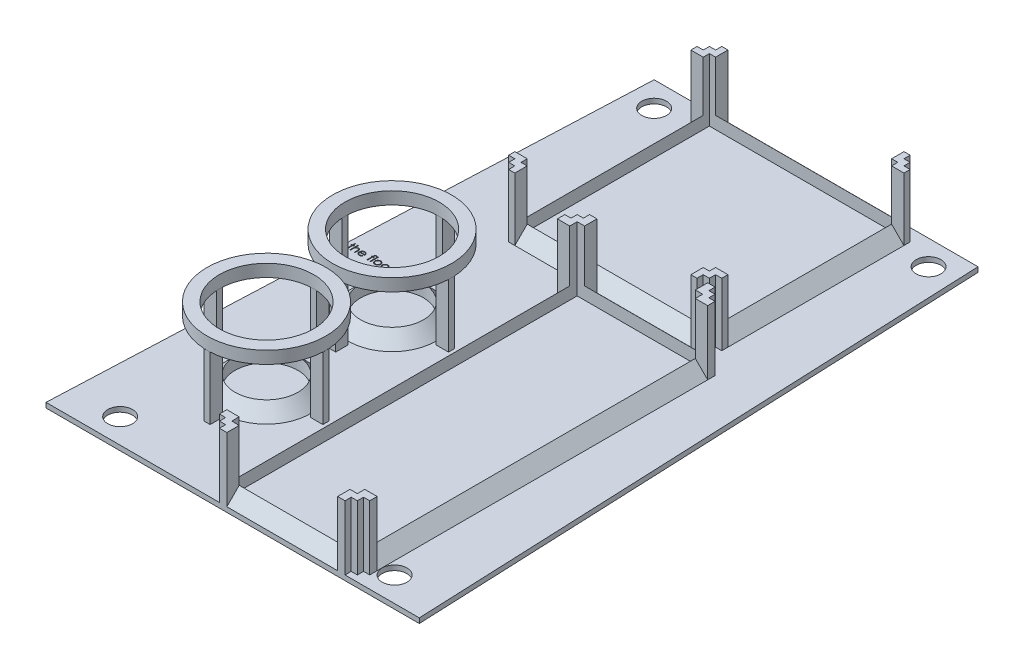
SolidWorks part; units mm, degrees
ref_plane "Front Plane" through (0, 0, 0) normal (0, 0, 1) x (1, 0, 0)
ref_plane "Top Plane" through (0, 0, 0) normal (0, 1, 0) x (1, 0, 0)
ref_plane "Right Plane" through (0, 0, 0) normal (1, 0, 0) x (0, 0, -1)
sketch "Sketch1" plane through (0, 0, 0) normal (0, 1, 0) x (1, 0, 0)
  line L0 (0, -118) -> (0, 118)
  line L1 (-65.5, 118) -> (65.5, 118)
  line L2 (-75.5, -118) -> (75.5, -118)
  line L3 (-65.5, 118) -> (-75.5, -118)
  line L4 (65.5, 118) -> (75.5, -118)
  point P4 (0, 0)
  point P8 (0, 118)
  point P11 (0, -118)
  dimension "D1" = 236
  dimension "D2" = 131
  dimension "D3" = 151
extrude "Boss-Extrude1" add sketch "Sketch1" along normal blind 2 contours L4 L1 L0 L2 | L1 L3 L2 L0
sketch "Sketch4" plane through (0, 0, 0) normal (0, -1, 0) x (1, 0, 0)
  text T0 "THE FLOOR FLOOR\r\n(bottom)"
extrude "Cut-Extrude3" cut sketch "Sketch4" against normal blind 0.5
sketch "Sketch5" plane through (0, 2, 0) normal (0, 1, 0) x (1, 0, 0)
  text T0 "the floor top!"
extrude "Cut-Extrude4" cut sketch "Sketch5" against normal blind 0.5
sketch "Sketch6" plane through (0, 2, 0) normal (0, 1, 0) x (1, 0, 0)
  line L0 (0, 74.85) -> (38.1, 74.85) construction
  line L1 (-38.1, 36.75) -> (38.1, 36.75)
  line L2 (-38.1, 36.75) -> (-38.1, 112.95)
  line L3 (-38.1, 112.95) -> (38.1, 112.95)
  line L4 (38.1, 36.75) -> (38.1, 112.95)
  line L5 (-38.1, 36.75) -> (38.1, 112.95) construction
  line L6 (-38.1, 112.95) -> (38.1, 36.75) construction
  line L7 (38.1, 74.85) -> (0, 74.85) construction
  line L8 (0, 74.85) -> (-38.1, 74.85) construction
  line L9 (-38.1, 74.85) -> (0, 74.85) construction
  line L10 (0, 74.85) -> (0, 112.95) construction
  line L11 (0, 112.95) -> (0, 36.75) construction
  line L12 (-65.5, 118) -> (65.5, 118) construction
  point P0 (0, 74.85)
  dimension "D1" = 76.2
  dimension "D2" = 5.05
ref_plane "Plane1" through (0, 0, -36.75) normal (0, 0, 1) x (1, 0, 0)
sketch "Sketch7" plane through (0, 0, -36.75) normal (0, 0, 1) x (1, 0, 0)
  line L0 (-38.1, 2) -> (-38.1, 7)
  line L1 (-38.1, 2) -> (38.1, 2) construction
  line L2 (-38.1, 7) -> (-43.1, 2)
  line L3 (-75.5, 2) -> (75.5, 2) construction
  line L4 (-43.1, 2) -> (-38.1, 2)
  dimension "D1" = 5
extrude "Boss-Extrude2" add sketch "Sketch7" against normal blind 76.2
mirror "Mirror1" about plane through (0, 0, 0) normal (1, 0, 0) of "Boss-Extrude2"
ref_plane "Plane2" through (0, 0, -74.85) normal (0, 0, 1) x (1, 0, 0)
ref_plane "Plane3" through (0, 0, 0) normal (1, 0, 0) x (0, 0, -1)
sketch "Sketch9" plane through (0, 0, 0) normal (1, 0, 0) x (0, 0, -1)
  line L0 (112.95, 2) -> (117.95, 2)
  line L1 (118, 2) -> (-118, 2) construction
  line L2 (112.95, 7) -> (112.95, 2) construction
  line L3 (112.95, 7) -> (112.95, 2)
  line L4 (112.95, 7) -> (117.95, 2)
extrude "Boss-Extrude7" add sketch "Sketch9" along normal mid plane 76
mirror "Mirror2" about plane through (0, 0, -74.85) normal (0, 0, 1) of "Boss-Extrude7"
sketch "Sketch11" plane through (0, 2, 0) normal (0, 1, 0) x (1, 0, 0)
  line L0 (-5.3455, -43.15) -> (-5.3455, 26.7)
  line L1 (-5.3455, 26.7) -> (45.4545, 26.7)
  line L2 (-5.3455, 26.7) -> (-5.3455, -113)
  line L3 (-5.3455, -113) -> (45.4545, -113)
  line L4 (45.4545, 26.7) -> (45.4545, -113)
  line L5 (-5.3455, 26.7) -> (20.0545, 26.7)
  line L7 (38, 31.75) -> (-38, 31.75) construction
  dimension "D1" = 139.7
  dimension "D2" = 50.8
  dimension "D3" = 69.85
  dimension "D4" = 5.05
ref_plane "Plane4" through (0, 0, 43.15) normal (0, 0, 1) x (1, 0, 0)
sketch "Sketch12" plane through (0, 0, 43.15) normal (0, 0, 1) x (1, 0, 0)
  line L0 (-10.3455, 2) -> (-5.3455, 2)
  line L1 (-38.1, 2) -> (38.1, 2) construction
  line L2 (-5.3455, 2) -> (45.4545, 2) construction
  line L3 (-5.3455, 2) -> (-5.3455, 7)
  line L4 (-5.3455, 7) -> (-10.3455, 2)
  dimension "D1" = 5
extrude "Boss-Extrude9" add sketch "Sketch12" along normal mid plane 139.7
ref_plane "Plane5" through (20.0545, 0, 0) normal (1, 0, 0) x (0, 0, -1)
mirror "Mirror4" about plane through (20.0545, 0, 0) normal (1, 0, 0) of "Boss-Extrude9"
sketch "Sketch13" plane through (20.0545, 0, 0) normal (1, 0, 0) x (0, 0, -1)
  line L0 (26.7, 2) -> (26.7, 7)
  line L1 (26.7, 7) -> (31.7, 2)
  line L2 (118, 2) -> (-118, 2) construction
  line L3 (31.7, 2) -> (26.7, 2)
  dimension "D1" = 5
extrude "Boss-Extrude11" add sketch "Sketch13" along normal mid plane 50
mirror "Mirror5" about plane through (0, 0, 43.15) normal (0, 0, 1) of "Boss-Extrude11"
sketch "Sketch14" plane through (0, 2, 0) normal (0, 1, 0) x (1, 0, 0)
  line L0 (45.0545, 31.7) -> (-4.9455, 31.7) construction
  line L1 (-5.3455, 26.7) -> (-2.3455, 26.7)
  line L2 (-5.3455, 26.7) -> (-5.3455, 31.7)
  line L3 (-5.3455, 31.7) -> (-2.3455, 31.7)
  line L4 (-2.3455, 26.7) -> (-2.3455, 31.7)
  line L6 (-10.3455, -113) -> (-10.3455, 26.7) construction
  line L7 (-5.3455, 26.7) -> (-10.3455, 26.7)
  line L8 (-5.3455, 26.7) -> (-5.3455, 23.7)
  line L9 (-5.3455, 23.7) -> (-10.3455, 23.7)
  line L10 (-10.3455, 26.7) -> (-10.3455, 23.7)
  line L12 (-5.3455, 26.7) -> (-7.8455, 26.7)
  line L13 (-5.3455, 26.7) -> (-5.3455, 29.2)
  line L14 (-5.3455, 29.2) -> (-7.8455, 29.2)
  line L15 (-7.8455, 26.7) -> (-7.8455, 29.2)
  dimension "D1" = 3
  dimension "D2" = 3
  dimension "D3" = 2.5
extrude "Boss-Extrude12" add sketch "Sketch14" along normal blind 26 contours L1 L4 L3 L2 | L15 L7 L2 L14 | L7 L10 L9 L8
mirror "Mirror6" about plane through (0, 0, 43.15) normal (0, 0, 1) of "Boss-Extrude12" second plane through (20.0545, 0, 0) second plane normal (1, 0, 0)
sketch "Sketch15" plane through (0, 2, 0) normal (0, 1, 0) x (1, 0, 0)
  line L0 (-35.7576, -17.75) -> (-48.4576, -17.75) construction
  circle A0 centre (-35.7576, -17.75) radius 12.7
  point P3 (-35.7576, -17.75)
  dimension "D1" = 25.4
  dimension "D3" = 25.4
ref_plane "Plane6" through (0, 0, 17.75) normal (0, 0, 1) x (1, 0, 0)
sketch "Sketch17" plane through (0, 0, 17.75) normal (0, 0, 1) x (1, 0, 0)
  line L0 (-35.7576, 2) -> (-48.4576, 2) construction
  line L1 (-35.7576, 2) -> (-48.4576, 2) construction
  line L2 (-48.4576, 2) -> (-48.4576, 7)
  line L3 (-48.4576, 7) -> (-53.4576, 2)
  line L4 (-53.4576, 2) -> (-48.4576, 2)
  line L5 (-35.7576, 2) -> (-35.7576, 11.5229) construction
  dimension "D1" = 90
  dimension "D2" = 5
revolve "Revolve1" add sketch "Sketch17" angle 360 about L5
ref_plane "Plane8" through (0, 0, 43.15) normal (0, 0, 1) x (1, 0, 0)
mirror "Mirror7" about plane through (0, 0, 43.15) normal (0, 0, 1) of "Revolve1"
sketch "Sketch19" plane through (0, 2, 0) normal (0, 1, 0) x (1, 0, 0)
  line L0 (-59.8076, -16.5) -> (-59.8076, -19)
  line L1 (-37.0076, -41.8) -> (-34.5076, -41.8)
  line L2 (-37.0076, -41.8) -> (-37.0076, -36.8)
  line L3 (-37.0076, -36.8) -> (-34.5076, -36.8)
  line L4 (-34.5076, -41.8) -> (-34.5076, -36.8)
  line L5 (-37.0076, -41.8) -> (-34.5076, -36.8) construction
  line L6 (-37.0076, -36.8) -> (-34.5076, -41.8) construction
  line L7 (-59.8076, -19) -> (-54.8076, -19)
  line L8 (-59.8076, -16.5) -> (-54.8076, -16.5)
  line L9 (-54.8076, -16.5) -> (-54.8076, -19)
  line L10 (-59.8076, -16.5) -> (-54.8076, -19) construction
  line L11 (-54.8076, -16.5) -> (-59.8076, -19) construction
  line L12 (-34.5076, 6.3) -> (-37.0076, 6.3)
  line L13 (-37.0076, 6.3) -> (-37.0076, 1.3)
  line L14 (-34.5076, 6.3) -> (-34.5076, 1.3)
  line L15 (-34.5076, 1.3) -> (-37.0076, 1.3)
  line L16 (-34.5076, 6.3) -> (-37.0076, 1.3) construction
  line L17 (-34.5076, 1.3) -> (-37.0076, 6.3) construction
  line L18 (-11.7076, -19) -> (-11.7076, -16.5)
  line L19 (-11.7076, -16.5) -> (-16.7076, -16.5)
  line L20 (-11.7076, -19) -> (-16.7076, -19)
  line L21 (-16.7076, -19) -> (-16.7076, -16.5)
  line L22 (-11.7076, -19) -> (-16.7076, -16.5) construction
  line L23 (-16.7076, -19) -> (-11.7076, -16.5) construction
  circle A0 centre (-35.7576, -17.75) radius 19.05
  point P3 (-35.7576, -39.3)
  point P8 (0, 0)
  point P9 (-35.7576, -39.3)
  point P10 (0, 0)
  point P11 (-57.3076, -17.75)
  point P16 (-35.7576, 3.8)
  point P21 (-14.2076, -17.75)
  point P26 (-35.7576, -17.75)
  dimension "D1" = 38.1
  dimension "D2" = 2.5
  dimension "D3" = 5
  dimension "D4" = 19.05
  dimension "D5" = 4
extrude "Boss-Extrude13" add sketch "Sketch19" along normal blind 25.4 contours L14 L15 L13 L12 | L19 L21 L20 L18 | L4 L3 L2 L1 | L7 L9 L8 L0
sketch "Sketch20" plane through (0, 27.4, 0) normal (0, 1, 0) x (1, 0, 0)
  circle A0 centre (-35.7576, -17.75) radius 19.05
  circle A1 centre (-35.7576, -17.75) radius 24.05
extrude "Boss-Extrude14" add sketch "Sketch20" along normal blind 5
mirror "Mirror8" about plane through (0, 0, 43.15) normal (0, 0, 1) of "Boss-Extrude13", "Boss-Extrude14"
sketch "Sketch21" plane through (0, 2, 0) normal (0, 1, 0) x (1, 0, 0)
  line L0 (-43.1, 112.95) -> (-43.1, 36.75) construction
  line L1 (-38.1, 112.95) -> (-43.1, 112.95)
  line L2 (-38.1, 112.95) -> (-38.1, 110.45)
  line L3 (-38.1, 110.45) -> (-43.1, 110.45)
  line L4 (-43.1, 112.95) -> (-43.1, 110.45)
  line L5 (38, 117.95) -> (-38, 117.95) construction
  line L6 (-38.1, 112.95) -> (-35.6, 112.95)
  line L7 (-38.1, 112.95) -> (-38.1, 117.95)
  line L8 (-38.1, 117.95) -> (-35.6, 117.95)
  line L9 (-35.6, 112.95) -> (-35.6, 117.95)
  line L10 (43.1, 112.95) -> (43.1, 36.75) construction
  line L11 (38.1, 112.95) -> (43.1, 112.95)
  line L12 (38.1, 112.95) -> (38.1, 110.45)
  line L13 (38.1, 110.45) -> (43.1, 110.45)
  line L14 (43.1, 112.95) -> (43.1, 110.45)
  line L15 (38, 31.75) -> (-38, 31.75) construction
  line L16 (38.1, 112.95) -> (35.6, 112.95)
  line L17 (38.1, 112.95) -> (38.1, 117.95)
  line L18 (38.1, 117.95) -> (35.6, 117.95)
  line L19 (35.6, 112.95) -> (35.6, 117.95)
  line L20 (38.1, 36.75) -> (43.1, 36.75)
  line L21 (38.1, 36.75) -> (38.1, 39.25)
  line L22 (38.1, 39.25) -> (43.1, 39.25)
  line L23 (43.1, 36.75) -> (43.1, 39.25)
  line L24 (38.1, 36.75) -> (35.6, 36.75)
  line L25 (38.1, 36.75) -> (38.1, 31.75)
  line L26 (38.1, 31.75) -> (35.6, 31.75)
  line L27 (35.6, 36.75) -> (35.6, 31.75)
  line L29 (-38.1, 36.75) -> (-43.1, 36.75)
  line L30 (-38.1, 36.75) -> (-38.1, 39.25)
  line L31 (-38.1, 39.25) -> (-43.1, 39.25)
  line L32 (-43.1, 36.75) -> (-43.1, 39.25)
  line L33 (-38.1, 36.75) -> (-35.6, 36.75)
  line L34 (-38.1, 36.75) -> (-38.1, 31.75)
  line L35 (-38.1, 31.75) -> (-35.6, 31.75)
  line L36 (-35.6, 36.75) -> (-35.6, 31.75)
  line L37 (-38.1, 112.95) -> (-40.6, 112.95)
  line L38 (-38.1, 112.95) -> (-38.1, 115.45)
  line L39 (-38.1, 115.45) -> (-40.6, 115.45)
  line L40 (-40.6, 112.95) -> (-40.6, 115.45)
  line L41 (38.1, 112.95) -> (40.6, 112.95)
  line L42 (38.1, 112.95) -> (38.1, 115.45)
  line L43 (38.1, 115.45) -> (40.6, 115.45)
  line L44 (40.6, 112.95) -> (40.6, 115.45)
  line L45 (38.1, 36.75) -> (40.6, 36.75)
  line L46 (38.1, 36.75) -> (38.1, 34.25)
  line L47 (38.1, 34.25) -> (40.6, 34.25)
  line L48 (40.6, 36.75) -> (40.6, 34.25)
  line L49 (-38.1, 36.75) -> (-40.6, 36.75)
  line L50 (-38.1, 36.75) -> (-38.1, 34.25)
  line L51 (-38.1, 34.25) -> (-40.6, 34.25)
  line L52 (-40.6, 36.75) -> (-40.6, 34.25)
  dimension "D1" = 2.5
  dimension "D2" = 2.5
  dimension "D3" = 2.5
  dimension "D4" = 2.5
  dimension "D5" = 2.5
  dimension "D6" = 2.5
  dimension "D7" = 2.5
  dimension "D8" = 2.5
  dimension "D9" = 2.5
extrude "Boss-Extrude15" add sketch "Sketch21" along normal blind 25.4 contours L6 L9 L8 L7 | L40 L1 L7 L39 | L1 L4 L3 L2 | L32 L29 L30 L31 | L29 L52 L51 L34 | L36 L33 L34 L35 | L20 L23 L22 L21 | L48 L20 L25 L47 | L24 L27 L26 L25 | L19 L16 L17 L18 | L14 L11 L12 L13 | L11 L44 L43 L17
ref_plane "Plane9" through (-49.8153, -41.61, 101.1) normal (1, 0, 0) x (0, -0.0295, -0.9996)
sketch "Sketch22" plane through (0, 2, 0) normal (0, 1, 0) x (1, 0, 0)
  line L0 (-65.5, 118) -> (-55.5, 118) construction
  line L1 (-65.5, 118) -> (65.5, 118) construction
  line L2 (-55.5, 118) -> (-55.5, 108) construction
  line L4 (0, 0) -> (10.4108, 0) construction
  line L5 (65.5, 118) -> (55.5, 118) construction
  line L6 (55.5, 118) -> (55.5, 108) construction
  circle A0 centre (-55.5, 108) radius 5
  circle A4 centre (55.5, 108) radius 5
  circle A5 centre (-55.5, -108) radius 5
  circle A6 centre (55.5, -108) radius 5
  dimension "D2" = 10
  dimension "D1" = 10
  dimension "D3" = 10
extrude "Cut-Extrude5" cut sketch "Sketch22" against normal through all
